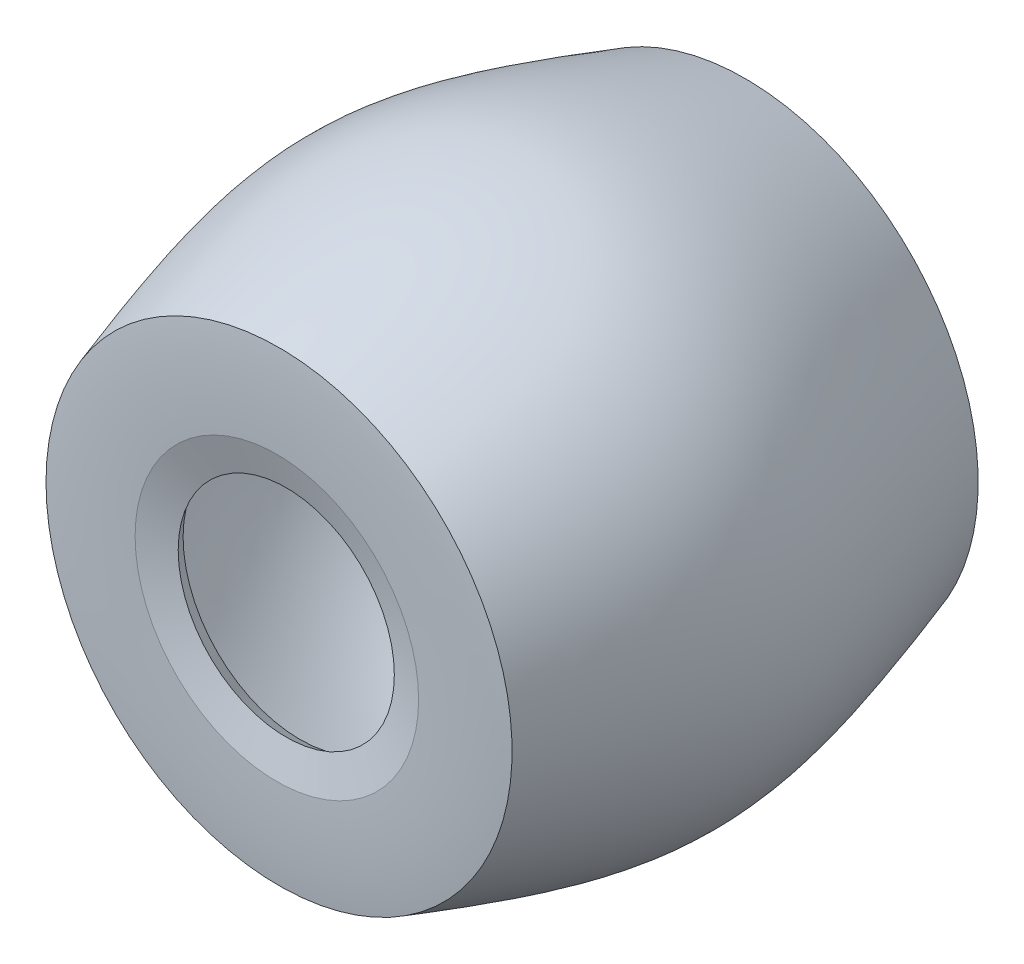
SolidWorks part; units mm, degrees
ref_plane "Front Plane" through (0, 0, 0) normal (0, 0, 1) x (1, 0, 0)
ref_plane "Top Plane" through (0, 0, 0) normal (0, 1, 0) x (1, 0, 0)
ref_plane "Right Plane" through (0, 0, 0) normal (1, 0, 0) x (0, 0, -1)
sketch "Sketch1" plane through (0, 0, 0) normal (1, 0, 0) x (0, 0, -1)
  line L0 (45.4446, 0) -> (-40.6948, 0) construction
  line L1 (0, 50) -> (0, -50) construction
  line L2 (50, 50) -> (-50, 50) construction
  line L3 (-50.4701, 30.412) -> (-48.4498, 23.1879)
  line L4 (-48.4498, 45.2464) -> (-48.4498, 29.9874)
  line L5 (-48.4498, 23.1879) -> (-45.4859, 25.1014)
  line L6 (48.4498, 23.1879) -> (45.4859, 25.1014)
  line L7 (48.4498, 45.2464) -> (48.4498, 29.9874)
  line L8 (50.4701, 30.412) -> (48.4498, 23.1879)
  line L10 (0, -50) -> (31.8556, -50) construction
  spline S0 degree 3 poles (-50, 50) (-4.9026, 64.7071) (4.9026, 64.7071) (50, 50) knots 0 0 0 0 1 1 1 1
  spline S1 degree 1 poles (-48.4498, 45.2464) (48.4498, 45.2464) knots 0 0 1 1 construction
  spline S2 degree 3 poles (-48.4498, 45.2464) (-47.7573, 45.4722) (-46.359, 45.9267) (-43.664, 46.7955) (-40.4097, 47.8301) (-36.6981, 48.9816) (-31.9836, 50.3995) (-26.5031, 51.9504) (-20.4895, 53.4589) (-14.9406, 54.6189) (-8.0222, 55.71) (0, 56.2439) (8.0222, 55.7099) (14.9406, 54.6189) (20.4895, 53.4589) (26.5031, 51.9504) (31.9836, 50.3995) (36.6981, 48.9816) (40.4097, 47.8301) (43.664, 46.7955) (46.359, 45.9267) (47.7573, 45.4722) (48.4498, 45.2464) knots 0 0 0 0 0.015625 0.03125 0.0625 0.09375 0.125 0.1875 0.25 0.3125 0.375 0.5 0.625 0.6875 0.75 0.8125 0.875 0.90625 0.9375 0.96875 0.984375 1 1 1 1
  spline S3 degree 2 poles (-50.4701, 30.412) (-50.8662, 41.5035) (-50, 50) knots 0 0 0 1 1 1
  spline S4 degree 1 poles (-48.4498, 29.9874) (-45.4859, 25.1014) knots 0 0 1 1
  spline S5 degree 1 poles (48.4498, 29.9874) (45.4859, 25.1014) knots 0 0 1 1
  spline S6 degree 2 poles (50.4701, 30.412) (50.8662, 41.5035) (50, 50) knots 0 0 0 1 1 1
  dimension "D1" = 100
  dimension "D2" = 100
  dimension "D3" = 5
revolve "Revolve1" add sketch "Sketch1" angle 360 about L0
